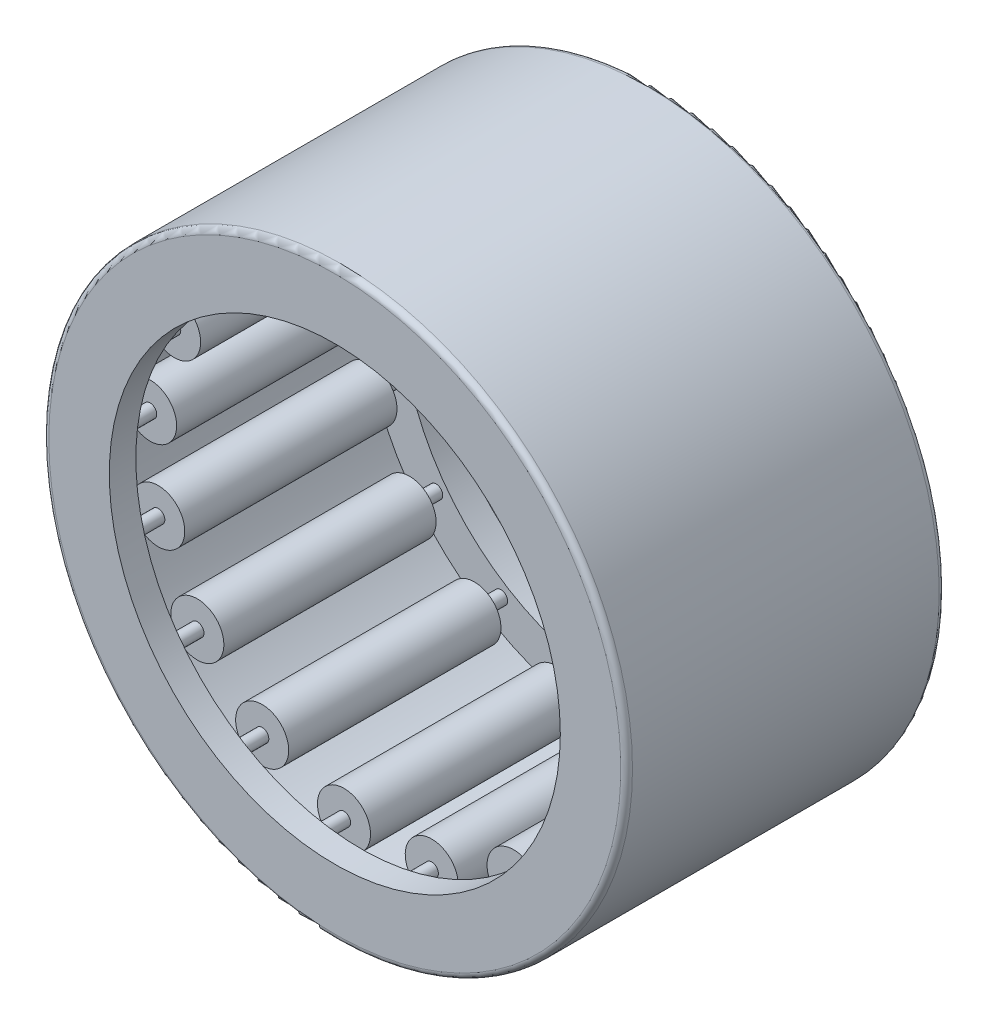
SolidWorks part; units mm, degrees
ref_plane "Front Plane" through (0, 0, 0) normal (0, 0, 1) x (1, 0, 0)
ref_plane "Top Plane" through (0, 0, 0) normal (0, 1, 0) x (1, 0, 0)
ref_plane "Right Plane" through (0, 0, 0) normal (1, 0, 0) x (0, 0, -1)
sketch "Sketch1" plane through (0, 0, 0) normal (1, 0, 0) x (0, 0, -1)
  line L0 (-6, 0) -> (6, 0) construction
  line L1 (0, 0) -> (0, 11) construction
  line L2 (-6, 0) -> (-6, 11) construction
  line L3 (-6, 11) -> (6, 11)
  line L4 (6, 11) -> (6, 0) construction
  line L5 (6, 0) -> (5, 0) construction
  line L6 (5, 0) -> (5, 10) construction
  line L7 (5, 10) -> (-5, 10)
  line L8 (-5, 10) -> (-5, 0) construction
  line L9 (-5, 0) -> (-6, 0) construction
  line L10 (-6, 11) -> (-6, 8.5)
  line L11 (-6, 8.5) -> (-5, 8.5)
  line L12 (-5, 8.5) -> (-5, 10)
  line L13 (5, 11) -> (5, 10) construction
  line L14 (5, 10) -> (5, 8.5)
  line L15 (5, 8.5) -> (6, 8.5)
  line L16 (6, 8.5) -> (6, 11)
  line L17 (5, 10) -> (5, 9) construction
  line L18 (5, 9) -> (5, 8) construction
  line L19 (5, -10) -> (5, -9) construction
  line L20 (5, -11) -> (5, -10) construction
  line L21 (6, -8.5) -> (6, -11) construction
  line L22 (5, -8.5) -> (6, -8.5) construction
  line L23 (5, -10) -> (5, -8.5) construction
  line L24 (-5, -8.5) -> (-5, -10) construction
  line L25 (-6, -8.5) -> (-5, -8.5) construction
  line L26 (-6, -11) -> (-6, -8.5) construction
  line L27 (5, -10) -> (-5, -10) construction
  line L28 (-6, -11) -> (6, -11) construction
  point P5 (0, 8)
  dimension "Width" = 12
  dimension "OD" = 22
  dimension "Shaft Dia" = 16
revolve "Revolve1" add sketch "Sketch1" angle 360 about L0
sketch "Sketch2" plane through (0, 0, 0) normal (1, 0, 0) x (0, 0, -1)
  line L0 (5, 10) -> (-5, 10) construction
  line L1 (-4, 9) -> (4, 9) construction
  line L2 (-4, 9) -> (-4, 10) construction
  line L3 (-4, 10) -> (4, 10)
  line L4 (4, 9) -> (4, 10) construction
  line L5 (5, 8.5) -> (6, 8.5) construction
  line L6 (-5, 9) -> (-4, 9) construction
  line L7 (4, 9) -> (5, 9) construction
  line L8 (-6, 8.5) -> (-5, 8.5) construction
  line L9 (-4, 9.25) -> (-4, 8.75) construction
  line L10 (-5, 9) -> (-5, 8.5) construction
  line L11 (-4, 10) -> (-4, 9.25)
  line L12 (4, 10) -> (4, 9.25)
  line L13 (4, 9.25) -> (-4, 9.25)
  line L14 (0, 10) -> (0, 8) construction
  line L15 (-5, 8.5) -> (-5, 10) construction
  line L16 (-4, 8.75) -> (-5, 8.75) construction
  line L17 (0, 0) -> (6, 0) construction
  line L18 (-4, -8.75) -> (-5, -8.75) construction
  line L19 (0, -10) -> (0, -8) construction
  line L20 (-5, -9) -> (-5, -8.5) construction
  line L21 (-4, -9.25) -> (-4, -8.75) construction
  line L22 (4, -9) -> (5, -9) construction
  line L23 (-5, -9) -> (-4, -9) construction
  line L24 (4, -9) -> (4, -10) construction
  line L25 (-4, -9) -> (-4, -10) construction
  line L26 (-4, -9) -> (4, -9) construction
  line L27 (4, -9.25) -> (-4, -9.25) construction
  line L28 (4, -10) -> (4, -9.25) construction
  line L29 (-4, -10) -> (-4, -9.25) construction
  line L30 (-4, -10) -> (4, -10) construction
  line L31 (6, -11) -> (6, 11) construction
  line L32 (5, 10) -> (5, 8.5) construction
  point P16 (0, 9)
revolve "Revolve2" add sketch "Sketch2" angle 360 about L1
sketch "Sketch3" plane through (0, 0, 0) normal (1, 0, 0) x (0, 0, -1)
  line L0 (5, 10) -> (5, 8.5) construction
  line L1 (-5, 9) -> (5, 9)
  line L2 (-5, 9) -> (-5, 9.25)
  line L3 (-5, 9.25) -> (5, 9.25)
  line L4 (5, 9) -> (5, 9.25)
  line L5 (0, 0) -> (6, 0) construction
  line L6 (6, -11) -> (6, 11) construction
  line L7 (5, -9) -> (5, -9.25) construction
  line L8 (-5, -9.25) -> (5, -9.25) construction
  line L9 (-5, -9) -> (-5, -9.25) construction
  line L10 (-5, -9) -> (5, -9) construction
revolve "Revolve3" add sketch "Sketch3" angle 360 about L1
ref_axis "Axis1" through (0, 0, -6) along (0, 0, 1)
pattern_circular "CirPattern1" count 17 every 21.176 about axis through (0, 0, -6) along (0, 0, 1) of bodies 166 167
fillet "Fillet1" radius 0.22 2 edges at (11, 0, -6) (11, 0, 6)
sketch "Sketch4" plane through (0, 0, 0) normal (1, 0, 0) x (0, 0, -1)
  line L0 (4, 10) -> (4, 9.25) construction
  line L1 (5.78, 8) -> (4, 8)
  line L2 (5.78, 8) -> (5.78, 8.5)
  line L3 (5.78, 8.5) -> (4, 8.5)
  line L4 (4, 8) -> (4, 8.5)
  line L5 (-6, 8.5) -> (-5, 8.5) construction
  line L6 (5.78, -11) -> (5.78, 11) construction
revolve "Revolve4" [suppressed] add sketch "Sketch4" angle 360 about L0
sketch "Sketch5" plane through (0, 0, 0) normal (1, 0, 0) x (0, 0, -1)
  line L0 (-5.78, 11) -> (-5.78, -11) construction
  line L1 (-4, 8) -> (-5.78, 8)
  line L2 (-4, 8) -> (-4, 8.5)
  line L3 (-4, 8.5) -> (-5.78, 8.5)
  line L4 (-5.78, 8) -> (-5.78, 8.5)
  line L5 (-4, 10) -> (-4, 9.25) construction
revolve "Revolve5" [suppressed] add sketch "Sketch5" angle 360 about L0
equation "\"Angle@CirPattern1\" = 360/\"Rollers@CirPattern1\""
equation "\"Rollers@CirPattern1\" = \"OD@Sketch1\"*.75"
equation "\"D1@Fillet1\" = \"OD@Sketch1\"*.01"
